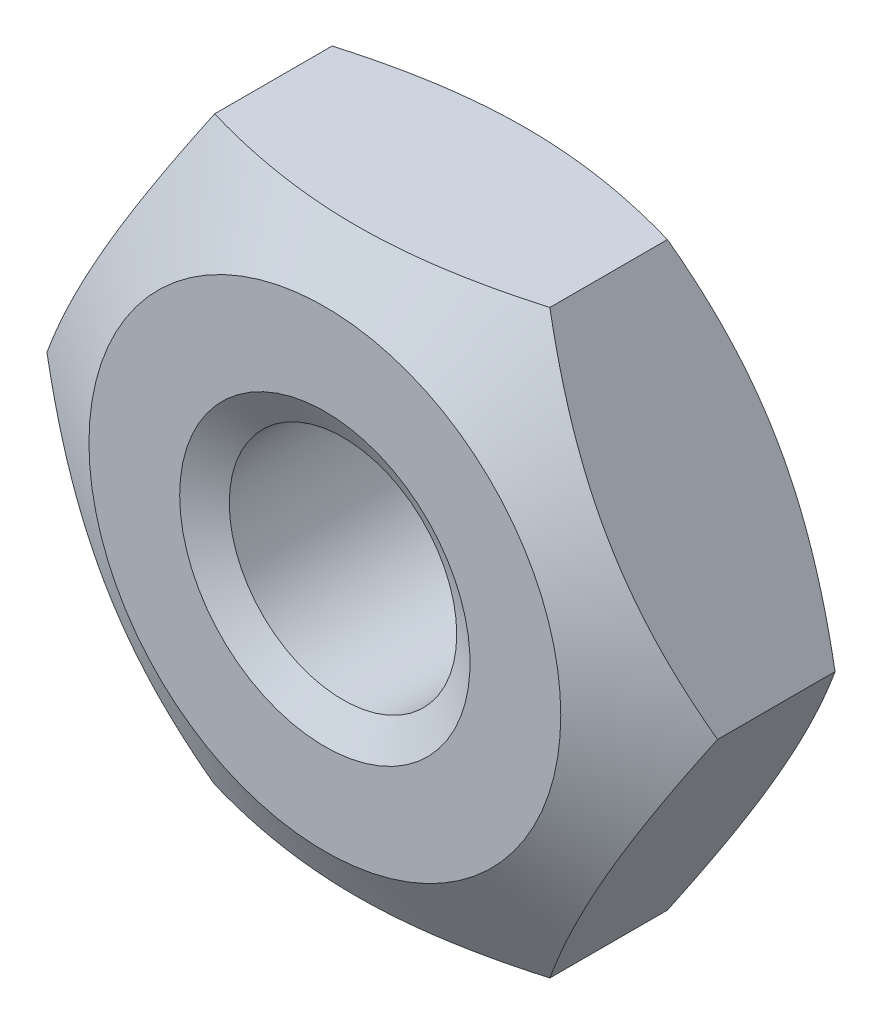
SolidWorks part; units mm, degrees
ref_plane "Front" through (0, 0, 0) normal (0, 0, 1) x (1, 0, 0)
ref_plane "Top" through (0, 0, 0) normal (0, 1, 0) x (1, 0, 0)
ref_plane "Right" through (0, 0, 0) normal (1, 0, 0) x (0, 0, -1)
sketch "Sketch1" plane through (0, 0, 0) normal (0, 0, 1) x (1, 0, 0)
  line L1 (2.3094, 0) -> (1.1547, 2)
  line L2 (1.1547, 2) -> (-1.1547, 2)
  line L3 (-1.1547, 2) -> (-2.3094, 0)
  line L4 (-2.3094, 0) -> (-1.1547, -2)
  line L5 (-1.1547, -2) -> (1.1547, -2)
  line L6 (1.1547, -2) -> (2.3094, 0)
  circle A0 centre (0, 0) radius 2 construction
  circle A1 centre (0, 0) radius 0.7835
extrude "BaseNut" add sketch "Sketch1" against normal blind 1.6
cosmetic thread "ThreadCosmetic1" [suppressed] parameters "D"=2
sketch "Sketch2" plane through (0, 0, 0) normal (0, 1, 0) x (1, 0, 0)
  line L0 (-2.3094, 1.6) -> (-1.625, 1.6)
  line L2 (-1.625, 1.6) -> (-2.3094, 1.2049)
  line L3 (-2.3094, 1.2049) -> (-2.3094, 1.6)
  line L4 (0, 3.3759) -> (0, -9.8171) construction
  line L6 (-9.7712, 0.8) -> (9.8853, 0.8) construction
  line L7 (-2.3094, 0.3951) -> (-2.3094, 0)
  line L8 (-1.625, 0) -> (-2.3094, 0.3951)
  line L9 (-2.3094, 0) -> (-1.625, 0)
  dimension "dw" = 59.25
  dimension "D1" = 30
  dimension "D2" = 16.7
revolve "Double-Chamfer" cut sketch "Sketch2" angle 360 about L4
chamfer "EndChamfer" distance 0.2165 angle 30 2 edges at (0.7835, 0, -1.6) (0.7835, 0, 0)
sketch "Sketch3" plane through (0, 0, 0) normal (0, 1, 0) x (1, 0, 0)
  line L0 (-0.971, 1.3835) -> (-0.7835, 1.2752)
  line L1 (-0.7835, 1.2752) -> (-0.567, 1.2752)
  line L2 (-0.567, 1.2752) -> (-0.567, 1.4917)
  line L3 (-0.567, 1.4917) -> (-0.7835, 1.4917)
  line L4 (-0.7835, 1.4917) -> (-0.971, 1.3835)
  line L5 (0, 7.4383) -> (0, 16.8806) construction
  dimension "D1" = 2.165
  dimension "D2" = 34.67
revolve "Cut-Revolve10" [suppressed] cut sketch "Sketch3" angle 360 about L5
pattern_linear "LPattern10" [suppressed] count 13 spacing 2.598 along (0, 0, -1)
equation "\"dw@Sketch2\" = \"s@Sketch1\"-0.75"
equation "\"D2@Sketch2\" = \"m@BaseNut\" / 2"
equation "\"D2@Sketch3\" = \"D@Sketch1\""
equation "\"D1@Sketch3\" =  (\"D@ThreadCosmetic1\"   - \"D@Sketch1\")  / 2"
equation "\"D3@LPattern10\" = \"D1@Sketch3\" * 1.2"
equation "\"D1@LPattern10\" = \"m@BaseNut\"/\"D3@LPattern10\""
